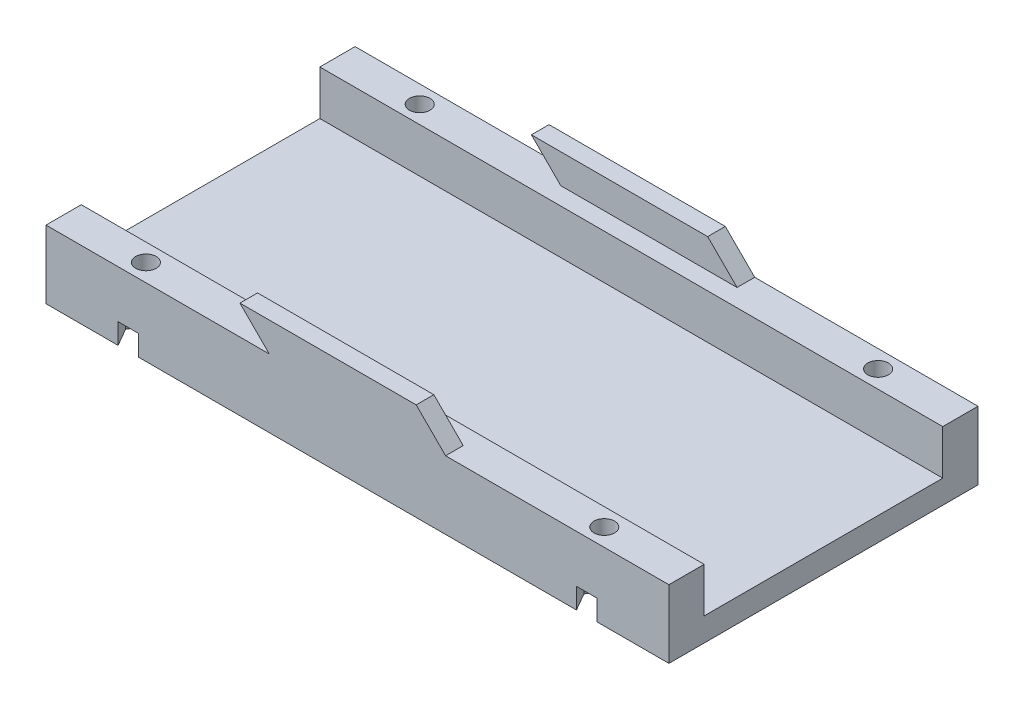
SolidWorks part; units mm, degrees
ref_plane "Front Plane" through (0, 0, 0) normal (0, 0, 1) x (1, 0, 0)
ref_plane "Top Plane" through (0, 0, 0) normal (0, 1, 0) x (1, 0, 0)
ref_plane "Right Plane" through (0, 0, 0) normal (1, 0, 0) x (0, 0, -1)
sketch "Sketch1" plane through (0, 0, 0) normal (0, 1, 0) x (1, 0, 0)
  line L1 (0, -13.3) -> (106, -13.3)
  line L2 (0, 0) -> (106, 0)
  line L3 (0, 0) -> (0, -4.8)
  line L4 (0, -4.8) -> (106, -4.8)
  line L5 (106, 0) -> (106, -4.8)
  line L6 (0, -13.3) -> (0, -4.8)
  line L7 (0, -4.8) -> (106, -4.8)
  line L8 (106, -13.3) -> (106, -4.8)
  line L9 (0, 0) -> (106, 0)
  line L10 (0, 0) -> (0, 8.5)
  line L11 (0, 8.5) -> (106, 8.5)
  line L12 (106, 0) -> (106, 8.5)
  line L13 (0, -22.7) -> (106, -22.7)
  line L14 (0, -22.7) -> (0, -13.3)
  line L15 (0, -13.3) -> (106, -13.3)
  line L16 (106, -22.7) -> (106, -13.3)
  line L17 (106, 8.5) -> (0, 8.5)
  line L18 (106, 8.5) -> (106, 17.9)
  line L19 (106, 17.9) -> (0, 17.9)
  line L20 (0, 8.5) -> (0, 17.9)
  line L21 (106, 17.9) -> (0, 17.9)
  line L22 (106, 17.9) -> (106, 23.9)
  line L23 (106, 23.9) -> (0, 23.9)
  line L24 (0, 17.9) -> (0, 23.9)
  line L25 (106, -28.7) -> (0, -28.7)
  line L26 (106, -28.7) -> (106, -22.7)
  line L27 (106, -22.7) -> (0, -22.7)
  line L28 (0, -28.7) -> (0, -22.7)
  dimension "D1" = 4.8
  dimension "D2" = 106
  dimension "D3" = 0
  dimension "D4" = 0
  dimension "D5" = 0
  dimension "D6" = 8.5
  dimension "D7" = 0
  dimension "D8" = 0
  dimension "D9" = 0
  dimension "D10" = 8.5
  dimension "D11" = 0
  dimension "D12" = 0
  dimension "D13" = 0
  dimension "D14" = 9.4
  dimension "D15" = 0
  dimension "D16" = 0
  dimension "D17" = 0
  dimension "D18" = 9.4
  dimension "D19" = 0
  dimension "D20" = 0
  dimension "D21" = 0
  dimension "D22" = 6
  dimension "D23" = 0
  dimension "D24" = 0
  dimension "D25" = 0
  dimension "D26" = 6
extrude "Boss-Extrude4" add sketch "Sketch1" along normal blind 4 contours L24 L19 L22 L23 | L20 L11 L18 L19 | L2 L12 L11 L10 | L5 L2 L3 L4 | L1 L8 L4 L6 | L13 L16 L1 L14 | L25 L28 L27 L26
sketch "Sketch4" plane through (0, 4, 0) normal (0, 1, 0) x (1, 0, 0)
  line L0 (106, -28.7) -> (106, 23.9) construction
  line L1 (0, -4.8) -> (106, -4.8)
  line L2 (0, -4.8) -> (0, 0)
  line L3 (0, 0) -> (106, 0)
  line L4 (106, -4.8) -> (106, 0)
  line L5 (0, -28.7) -> (0, 23.9) construction
  line L6 (106, 23.9) -> (0, 23.9) construction
  line L7 (106, -28.7) -> (0, -28.7) construction
  line L9 (106, 8.5) -> (0, 8.5)
  line L10 (106, 8.5) -> (106, 0)
  line L11 (106, 0) -> (0, 0)
  line L12 (0, 8.5) -> (0, 0)
  line L13 (106, -4.8) -> (0, -4.8)
  line L14 (106, -4.8) -> (106, -13.3)
  line L15 (106, -13.3) -> (0, -13.3)
  line L16 (0, -4.8) -> (0, -13.3)
  line L17 (106, 23.9) -> (0, 23.9)
  line L18 (106, 23.9) -> (106, 17.9)
  line L19 (106, 17.9) -> (0, 17.9)
  line L20 (0, 23.9) -> (0, 17.9)
  line L21 (106, -22.7) -> (0, -22.7)
  line L22 (106, -22.7) -> (106, -28.7)
  line L23 (106, -28.7) -> (0, -28.7)
  line L24 (0, -22.7) -> (0, -28.7)
  line M5 (0, 23.9) -> (0, -28.7)
  line M6 (0, -28.7) -> (106, -28.7)
  line M7 (106, -28.7) -> (106, 23.9)
  line M8 (106, 23.9) -> (0, 23.9)
  dimension "D1" = 0
  dimension "D2" = 23.9
  dimension "D3" = 23.9
  dimension "D4" = 0
  dimension "D5" = 8.5
  dimension "D6" = 8.5
  dimension "D7" = 6
  dimension "D8" = 6
sketch "Sketch5" plane through (0, 4, 0) normal (0, 1, 0) x (1, 0, 0)
  line L0 (0, -28.7) -> (0, 23.9) construction
  line L1 (106, 23.9) -> (0, 23.9)
  line L2 (106, 23.9) -> (106, 17.9)
  line L3 (106, 17.9) -> (0, 17.9)
  line L4 (0, 23.9) -> (0, 17.9)
  line L5 (0, -28.7) -> (0, 23.9) construction
  line L6 (106, -28.7) -> (0, -28.7)
  line L7 (106, -28.7) -> (106, -22.7)
  line L8 (106, -22.7) -> (0, -22.7)
  line L9 (0, -28.7) -> (0, -22.7)
  dimension "D1" = 6
  dimension "D2" = 6
extrude "Boss-Extrude5" add sketch "Sketch5" along normal blind 7.6
extrude "Boss-Extrude6" add sketch "Sketch4" along normal blind 7.6 contours L19 M7 M8 M5 | L21 M7 M5 M6
sketch "Sketch6" plane through (0, 11.6, 0) normal (0, 1, 0) x (1, 0, 0)
  line L0 (106, 17.9) -> (106, 23.9) construction
  line L1 (106, 23.9) -> (0, 23.9) construction
  line L2 (0, -28.7) -> (106, -28.7) construction
  line L3 (106, -28.7) -> (106, -22.7) construction
  line L4 (0, 23.9) -> (0, 17.9) construction
  line L5 (0, 17.9) -> (106, 17.9) construction
  line L6 (0, -22.7) -> (0, -28.7) construction
  circle A0 centre (92, 20.9) radius 1.75
  circle A1 centre (92, -25.7) radius 1.75
  circle A2 centre (14, 20.9) radius 1.75
  circle A3 centre (14, -25.7) radius 1.75
  point P4 (106, 20.9)
  dimension "D1" = 3.5
  dimension "D6" = 3.5
  dimension "D7" = 3.5
  dimension "D10" = 3.5
  dimension "D2" = 14
  dimension "D3" = 3
  dimension "D4" = 3
  dimension "D5" = 14
  dimension "D8" = 14
  dimension "D9" = 3
  dimension "D11" = 14
  dimension "D12" = 3
extrude "Cut-Extrude1" cut sketch "Sketch6" against normal blind 20
sketch "Sketch7" plane through (0, 0, 0) normal (0, -1, 0) x (1, 0, 0)
  line L0 (106, 28.7) -> (0, 28.7) construction
  line L1 (17.4641, 25.7) -> (15.7321, 28.7)
  line L2 (15.7321, 28.7) -> (12.2679, 28.7)
  line L3 (12.2679, 28.7) -> (10.5359, 25.7)
  line L4 (10.5359, 25.7) -> (12.2679, 22.7)
  line L5 (12.2679, 22.7) -> (15.7321, 22.7)
  line L6 (15.7321, 22.7) -> (17.4641, 25.7)
  line L8 (95.4641, 25.7) -> (93.7321, 28.7)
  line L9 (93.7321, 28.7) -> (90.2679, 28.7)
  line L10 (90.2679, 28.7) -> (88.5359, 25.7)
  line L11 (88.5359, 25.7) -> (90.2679, 22.7)
  line L12 (90.2679, 22.7) -> (93.7321, 22.7)
  line L13 (93.7321, 22.7) -> (95.4641, 25.7)
  line L14 (106, -23.9) -> (0, -23.9) construction
  line L15 (17.4641, -20.9) -> (15.7321, -17.9)
  line L16 (15.7321, -17.9) -> (12.2679, -17.9)
  line L17 (12.2679, -17.9) -> (10.5359, -20.9)
  line L18 (10.5359, -20.9) -> (12.2679, -23.9)
  line L19 (12.2679, -23.9) -> (15.7321, -23.9)
  line L20 (15.7321, -23.9) -> (17.4641, -20.9)
  line L22 (95.4641, -20.9) -> (93.7321, -17.9)
  line L23 (93.7321, -17.9) -> (90.2679, -17.9)
  line L24 (90.2679, -17.9) -> (88.5359, -20.9)
  line L25 (88.5359, -20.9) -> (90.2679, -23.9)
  line L26 (90.2679, -23.9) -> (93.7321, -23.9)
  line L27 (93.7321, -23.9) -> (95.4641, -20.9)
  circle A0 centre (14, 25.7) radius 3 construction
  circle A1 centre (92, 25.7) radius 3 construction
  circle A2 centre (14, -20.9) radius 3 construction
  circle A3 centre (92, -20.9) radius 3 construction
  dimension "D1" = 6
  dimension "D3" = 6
  dimension "D5" = 6
  dimension "D7" = 6
  dimension "D2" = 3
  dimension "D4" = 3
  dimension "D6" = 3
  dimension "D8" = 3
extrude "Cut-Extrude3" cut sketch "Sketch7" against normal blind 3.5
sketch "Sketch8" plane through (0, 0, 28.7) normal (0, 0, 1) x (1, 0, 0)
  line L0 (38, 11.6) -> (33, 16.6)
  line L1 (38, 11.6) -> (68, 11.6)
  line L2 (33, 16.6) -> (63, 16.6)
  line L3 (68, 11.6) -> (63, 16.6)
  line L4 (0, 11.6) -> (106, 11.6) construction
  line L5 (0, 11.6) -> (0, 0) construction
  point P8 (-9.6062, 8.2864)
  dimension "D1" = 0
  dimension "D2" = 5
  dimension "D3" = 30
  dimension "D4" = 38
  dimension "D5" = 315
extrude "Boss-Extrude8" add sketch "Sketch8" against normal blind 3
sketch "Sketch9" plane through (0, 0, -23.9) normal (0, 0, -1) x (-1, 0, 0)
  line L0 (-68, 11.6) -> (-63, 16.6)
  line L1 (-68, 11.6) -> (-38, 11.6)
  line L2 (-63, 16.6) -> (-33, 16.6)
  line L3 (-38, 11.6) -> (-33, 16.6)
  line L4 (-106, 11.6) -> (0, 11.6) construction
  dimension "D1" = 0
  dimension "D2" = 5
  dimension "D3" = 30
  dimension "D4" = 135
  dimension "D5" = 38
extrude "Boss-Extrude9" add sketch "Sketch9" against normal blind 3
